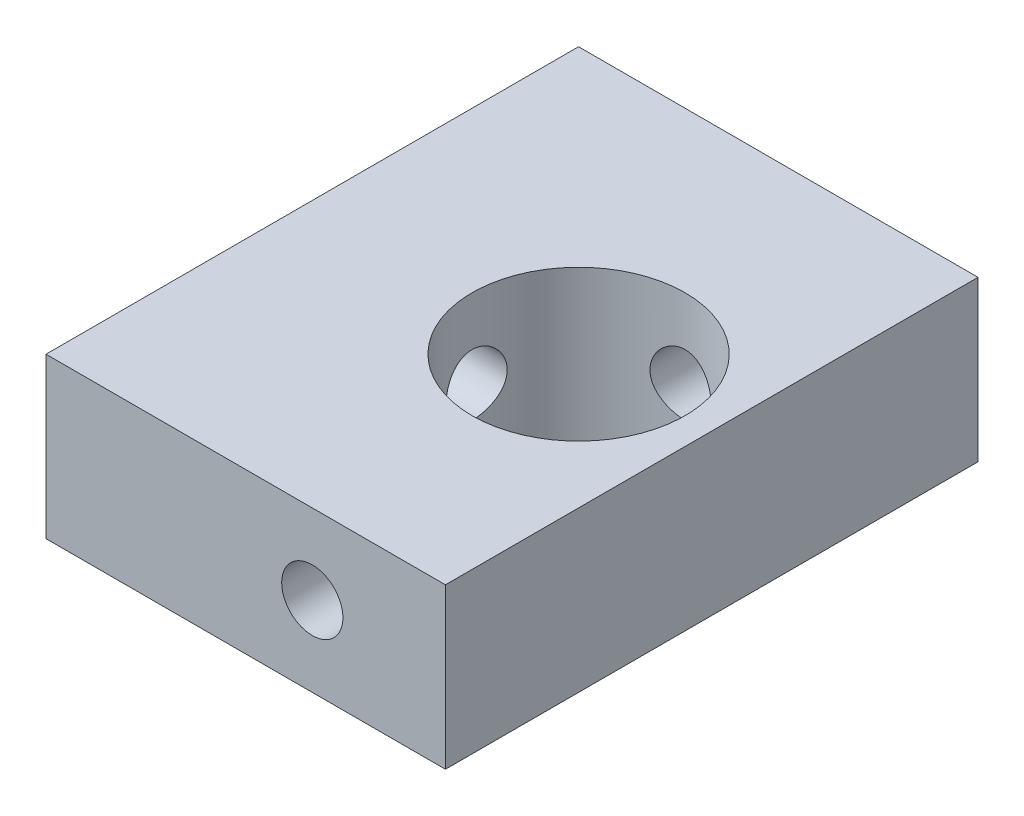
SolidWorks part; units mm, degrees
ref_plane "Front Plane" through (0, 0, 0) normal (0, 0, 1) x (1, 0, 0)
ref_plane "Top Plane" through (0, 0, 0) normal (0, 1, 0) x (1, 0, 0)
ref_plane "Right Plane" through (0, 0, 0) normal (1, 0, 0) x (0, 0, -1)
sketch "Sketch1" plane through (0, 0, 0) normal (0, 0, 1) x (1, 0, 0)
  line L1 (0, 0) -> (15, 0)
  line L2 (0, 0) -> (0, 6)
  line L3 (0, 6) -> (15, 6)
  line L4 (15, 0) -> (15, 6)
  circle A0 centre (10, 3) radius 1.15
  dimension "D3" = 2.3
  dimension "D1" = 6
  dimension "D2" = 15
  dimension "D4" = 3
  dimension "D5" = 10
extrude "Boss-Extrude1" add sketch "Sketch1" along normal blind 20
sketch "Sketch2" plane through (0, 0, 0) normal (0, -1, 0) x (1, 0, 0)
  line L0 (0, 20) -> (0, 0) construction
  line L1 (0, 0) -> (15, 0) construction
  circle A0 centre (10, 10) radius 4
  dimension "D1" = 8
  dimension "D2" = 10
  dimension "D3" = 10
extrude "Cut-Extrude2" cut sketch "Sketch2" against normal blind 20
sketch "Sketch4" plane through (0, 0, 0) normal (-1, 0, 0) x (0, 0, 1)
  line L0 (20, 6) -> (20, 0) construction
  line L1 (20, 6) -> (0, 6) construction
  circle A0 centre (10, 3) radius 1.15
  dimension "D1" = 2.3
  dimension "D2" = 10
  dimension "D3" = 3
extrude "Cut-Extrude3" cut sketch "Sketch4" against normal up to next
